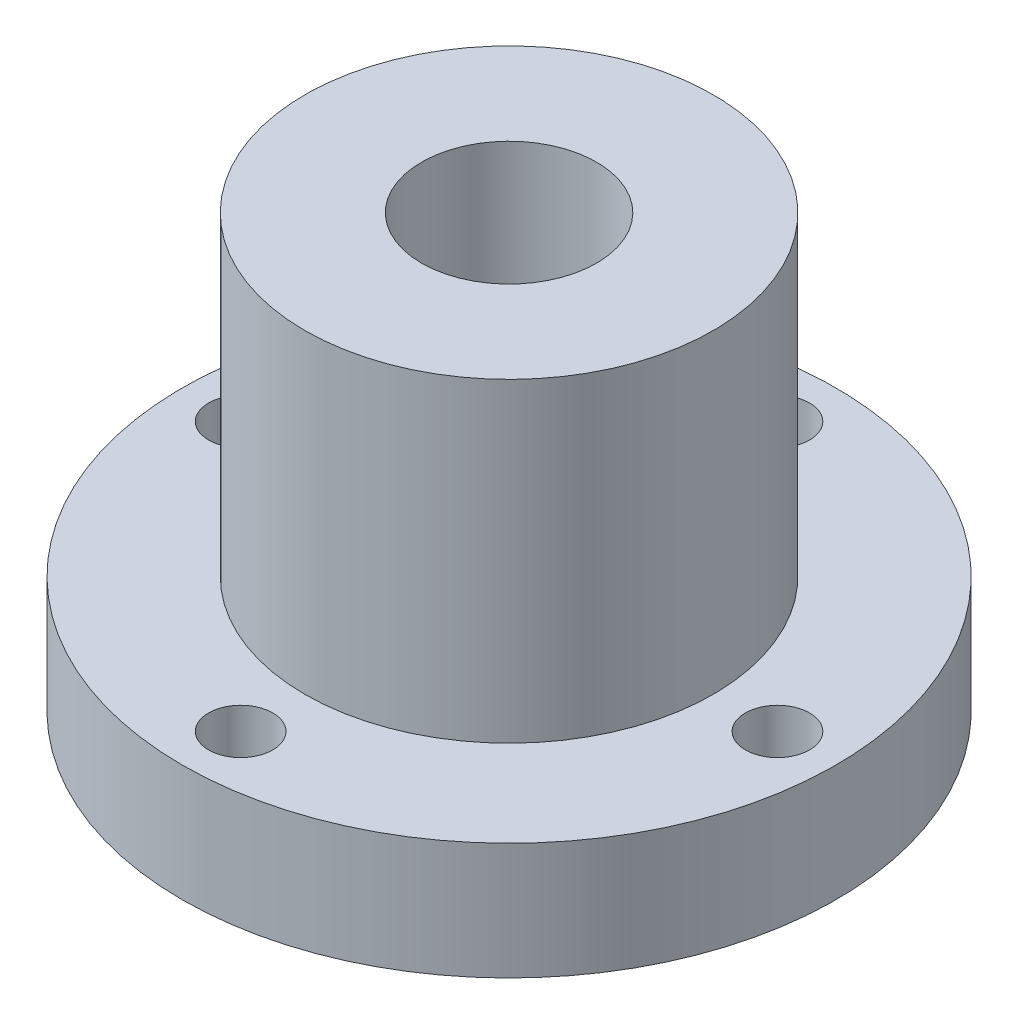
SolidWorks part; units mm, degrees
ref_plane "前视基准面" through (0, 0, 0) normal (0, 0, 1) x (1, 0, 0)
ref_plane "上视基准面" through (0, 0, 0) normal (0, 1, 0) x (1, 0, 0)
ref_plane "右视基准面" through (0, 0, 0) normal (1, 0, 0) x (0, 0, -1)
sketch "草图1" plane through (0, 0, 0) normal (0, 1, 0) x (1, 0, 0)
  circle A0 centre (0, 0) radius 7.5
  circle A1 centre (0, 0) radius 28
  dimension "D1" = 15
  dimension "D2" = 56
extrude "凸台-拉伸1" add sketch "草图1" along normal blind 10
ref_plane "基准面1" through (0, 10, 0) normal (0, 1, 0) x (1, 0, 0)
sketch "草图2" plane through (0, 10, 0) normal (0, 1, 0) x (1, 0, 0)
  circle A0 centre (0, 0) radius 7.5
  circle A1 centre (0, 0) radius 17.5
  dimension "D1" = 15
  dimension "D2" = 35
extrude "凸台-拉伸2" add sketch "草图2" along normal blind 27
sketch "草图3" plane through (0, 10, 0) normal (0, 1, 0) x (1, 0, 0)
  circle A0 centre (0, 0) radius 23 construction
  circle A1 centre (0, 23) radius 2.75
  circle A2 centre (23, 0) radius 2.75
  circle A3 centre (0, -23) radius 2.75
  circle A4 centre (-23, 0) radius 2.75
  point P14 (0, 0)
  dimension "D1" = 46
  dimension "D2" = 5.5
  dimension "D3" = 4
extrude "切除-拉伸1" cut sketch "草图3" against normal blind 27
